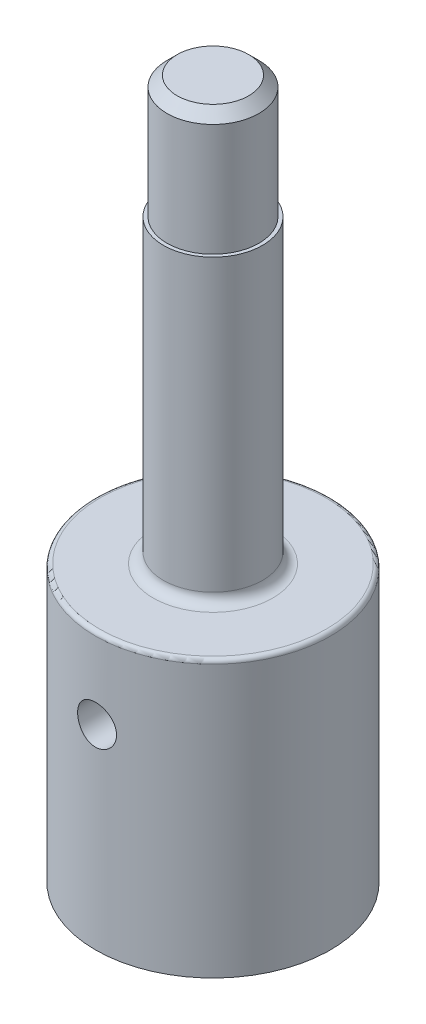
SolidWorks part; units mm, degrees
ref_plane "Alzado" through (0, 0, 0) normal (0, 0, 1) x (1, 0, 0)
ref_plane "Planta" through (0, 0, 0) normal (0, 1, 0) x (1, 0, 0)
ref_plane "Vista lateral" through (0, 0, 0) normal (1, 0, 0) x (0, 0, -1)
sketch "Croquis1" plane through (0, 0, 0) normal (0, 0, 1) x (1, 0, 0)
  line L0 (0, 96.1875) -> (0, -100.6875) construction
  line L1 (0, 175.625) -> (22.5, 175.625)
  line L2 (22.5, 175.625) -> (22.5, 115.625)
  line L3 (22.5, 115.625) -> (24.25, 115.625)
  line L4 (24.25, 115.625) -> (24.25, -31.375)
  line L5 (24.25, -31.375) -> (57.5, -31.375)
  line L6 (57.5, -31.375) -> (57.5, -166.375)
  line L7 (57.5, -166.375) -> (35.25, -166.375)
  line L8 (35.25, -166.375) -> (35.25, -46.375)
  line L9 (35.25, -46.375) -> (0, -46.375)
  line L10 (0, -46.375) -> (0, 175.625)
  dimension "D1" = 22.5
  dimension "D2" = 35.25
  dimension "48.5/2" = 24.25
  dimension "115/2" = 57.5
  dimension "D3" = 60
  dimension "D4" = 15
  dimension "147" = 147
  dimension "D5" = 135
revolve "Revolución2" add sketch "Croquis1" angle 360 about L0
fillet "Redondeo1" radius 5 1 edges at (0, -31.375, 24.25)
fillet "Redondeo2" radius 2 1 edges at (0, -46.375, 35.25)
sketch "Croquis2" plane through (0, 0, 0) normal (0, 0, 1) x (1, 0, 0)
  line L0 (-33.25, -46.375) -> (33.25, -46.375) construction
  circle A0 centre (0, -70.9) radius 9.525
  dimension "D1" = 19.05
  dimension "34.05" = 24.525
extrude "Cortar-Extruir1" cut sketch "Croquis2" against normal mid plane 120
fillet "Redondeo3" radius 2 1 edges at (0, -31.375, 57.5)
chamfer "Chaflán1" distance 5 angle 45 1 edges at (0, 175.625, 22.5)
